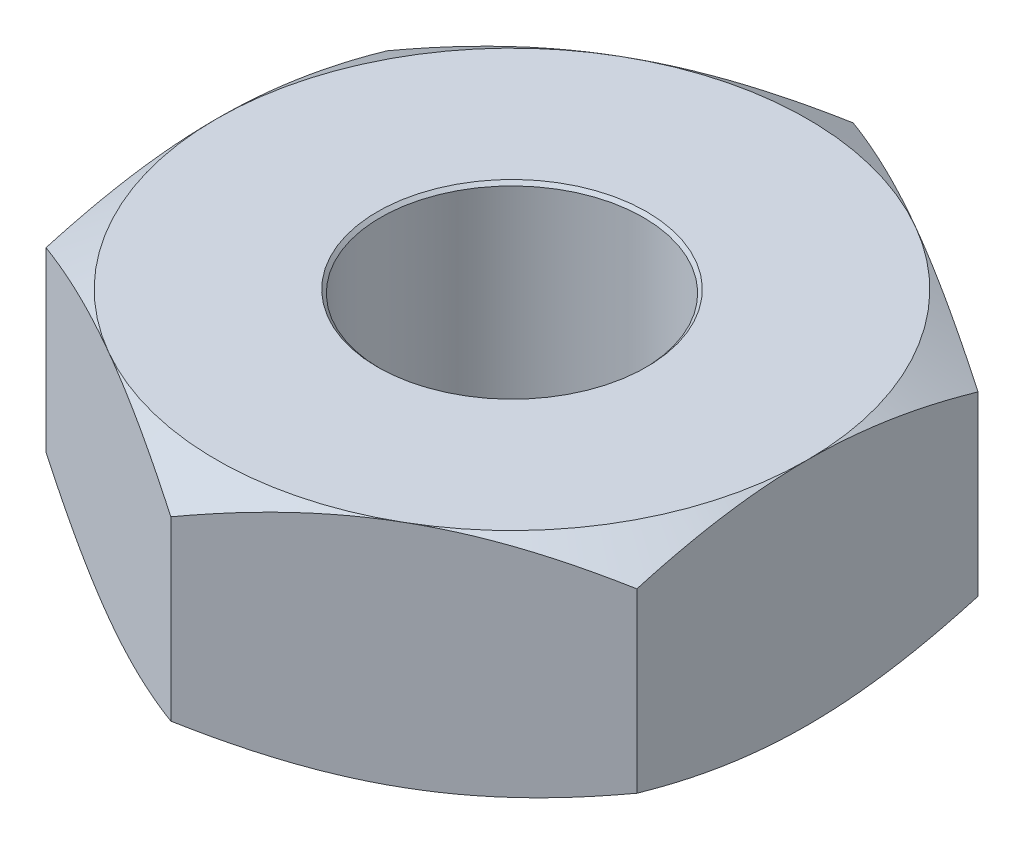
SolidWorks part; units mm, degrees
material "AISI 1045 Acero estirado en frío"
ref_plane "Front Plane" through (0, 0, 0) normal (0, 0, 1) x (1, 0, 0)
ref_plane "Top Plane" through (0, 0, 0) normal (0, 1, 0) x (1, 0, 0)
ref_plane "Right Plane" through (0, 0, 0) normal (1, 0, 0) x (0, 0, -1)
sketch "Sketch1" plane through (0, 0, 0) normal (0, 1, 0) x (1, 0, 0)
  line L1 (0, -2.5981) -> (2.25, -1.299)
  line L2 (2.25, -1.299) -> (2.25, 1.299)
  line L3 (2.25, 1.299) -> (0, 2.5981)
  line L4 (0, 2.5981) -> (-2.25, 1.299)
  line L5 (-2.25, 1.299) -> (-2.25, -1.299)
  line L6 (-2.25, -1.299) -> (0, -2.5981)
  circle A0 centre (0, 0) radius 2.25 construction
  circle A1 centre (0, 0) radius 1
  dimension "D1" = 4.5
  dimension "D2" = 2
extrude "Boss-Extrude1" add sketch "Sketch1" along normal blind 1.75
sketch "Sketch2" plane through (0, 1.75, 0) normal (0, 1, 0) x (1, 0, 0)
  circle A0 centre (0, 0) radius 2.25 construction
  circle A1 centre (0, 0) radius 2.25
extrude "Cut-Extrude1" cut sketch "Sketch2" against normal blind 1.75 draft 60 flip side to cut
sketch "Sketch3" plane through (0, 0, 0) normal (0, -1, 0) x (1, 0, 0)
  circle A0 centre (0, 0) radius 2.25 construction
  circle A1 centre (0, 0) radius 2.25
extrude "Cut-Extrude3" cut sketch "Sketch3" against normal blind 1.75 draft 60 flip side to cut
chamfer "Chamfer1" distance 0.025 angle 45 2 edges at (0, 0, 1) (0, 1.75, 1)
